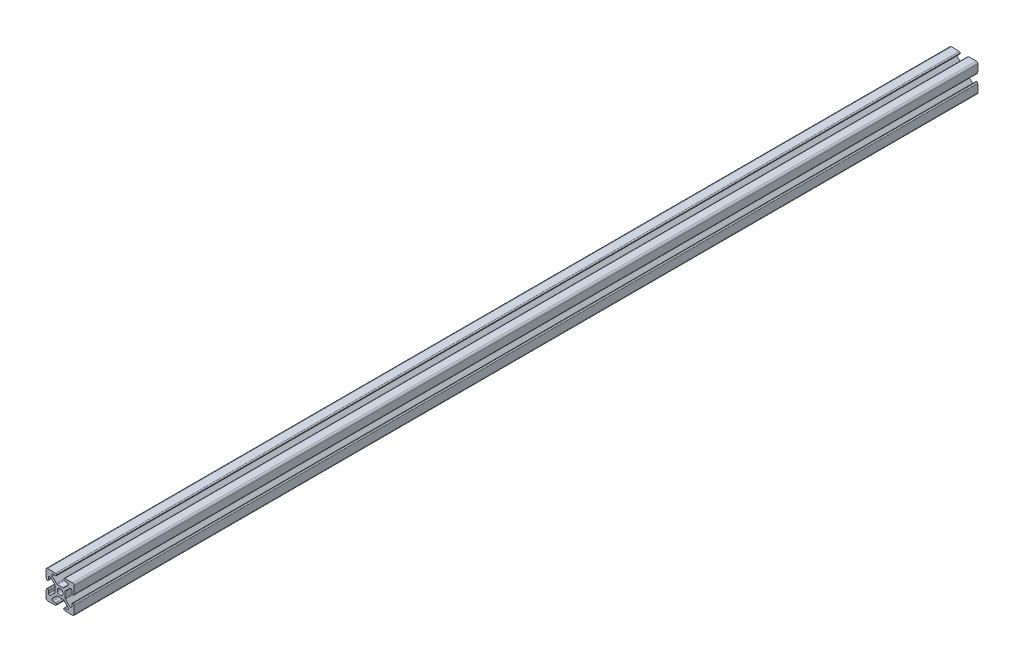
SolidWorks part; units mm, degrees
material "6061 Alloy"
ref_plane "Front Plane" through (0, 0, 0) normal (0, 0, 1) x (1, 0, 0)
ref_plane "Top Plane" through (0, 0, 0) normal (0, 1, 0) x (1, 0, 0)
ref_plane "Right Plane" through (0, 0, 0) normal (1, 0, 0) x (0, 0, -1)
sketch "Sketch1" plane through (0, 0, 0) normal (0, 0, 1) x (1, 0, 0)
  line L1 (3.2385, -11.4554) -> (3.2385, -11.4907)
  line L2 (-7.1065, 8.6691) -> (-3.2584, 4.821)
  line L3 (-3.2385, 11.4907) -> (-3.2385, 11.4554)
  line L6 (-4.2037, 10.4902) -> (-6.3521, 10.4902)
  line L7 (-11.176, 12.7) -> (-4.17, 12.4553)
  line L8 (11.4554, 3.2385) -> (11.4907, 3.2385)
  line L9 (11.4554, -3.2385) -> (11.4907, -3.2385)
  line L11 (-4.821, 3.2584) -> (-8.6691, 7.1065)
  line L12 (-10.4902, 6.3521) -> (-10.4902, 4.2037)
  line L13 (-12.7, 11.176) -> (-12.4553, 4.17)
  line L15 (-4.5085, -2.504) -> (-4.5085, 2.504)
  line L16 (6.3521, -10.4902) -> (4.2037, -10.4902)
  line L22 (-2.504, 4.5085) -> (2.504, 4.5085)
  line L23 (-3.2584, -4.821) -> (-7.1065, -8.6691)
  line L24 (-11.176, -12.7) -> (-4.17, -12.4553)
  line L25 (-12.7, -11.176) -> (-12.4553, -4.17)
  line L26 (-10.4902, -4.2037) -> (-10.4902, -6.3521)
  line L27 (-8.6691, -7.1065) -> (-4.821, -3.2584)
  line L36 (8.6691, -7.1065) -> (4.821, -3.2584)
  line L38 (10.4902, -4.2037) -> (10.4902, -6.3521)
  line L39 (12.7, -11.176) -> (12.4553, -4.17)
  line L42 (11.176, -12.7) -> (4.17, -12.4553)
  line L43 (3.2584, -4.821) -> (7.1065, -8.6691)
  line L47 (4.5085, -2.504) -> (4.5085, 2.504)
  line L48 (12.7, 11.176) -> (12.4553, 4.17)
  line L49 (10.4902, 6.3521) -> (10.4902, 4.2037)
  line L50 (4.821, 3.2584) -> (8.6691, 7.1065)
  line L52 (2.504, -4.5085) -> (-2.504, -4.5085)
  line L56 (11.176, 12.7) -> (4.17, 12.4553)
  line L57 (4.2037, 10.4902) -> (6.3521, 10.4902)
  line L59 (-6.3521, -10.4902) -> (-4.2037, -10.4902)
  line L60 (3.2385, 11.4907) -> (3.2385, 11.4554)
  line L61 (7.1065, 8.6691) -> (3.2584, 4.821)
  line L66 (-11.4554, -3.2385) -> (-11.4907, -3.2385)
  line L68 (-11.4554, 3.2385) -> (-11.4907, 3.2385)
  line L74 (-3.2385, -11.4554) -> (-3.2385, -11.4907)
  arc A1 (-3.2385, 11.4907) -> (-4.17, 12.4553) centre (-4.2037, 11.4907) ccw
  arc A4 (-4.2037, 10.4902) -> (-3.2385, 11.4554) centre (-4.2037, 11.4554) ccw
  arc A6 (-6.3521, 10.4902) -> (-7.1065, 8.6691) centre (-6.3521, 9.4234) ccw
  arc A8 (-12.4553, 4.17) -> (-11.4907, 3.2385) centre (-11.4907, 4.2037) ccw
  arc A9 (-11.176, 12.7) -> (-12.7, 11.176) centre (-11.176, 11.176) ccw
  arc A12 (-8.6691, 7.1065) -> (-10.4902, 6.3521) centre (-9.4234, 6.3521) ccw
  arc A13 (-11.4554, 3.2385) -> (-10.4902, 4.2037) centre (-11.4554, 4.2037) ccw
  arc A16 (-4.821, -3.2584) -> (-4.5085, -2.504) centre (-5.5753, -2.504) ccw
  arc A17 (-4.5085, 2.504) -> (-4.821, 3.2584) centre (-5.5753, 2.504) ccw
  arc A22 (3.2584, 4.821) -> (2.504, 4.5085) centre (2.504, 5.5753) cw
  arc A23 (10.4902, -6.3521) -> (8.6691, -7.1065) centre (9.4234, -6.3521) cw
  arc A24 (10.4902, -4.2037) -> (11.4554, -3.2385) centre (11.4554, -4.2037) cw
  arc A25 (11.4907, -3.2385) -> (12.4553, -4.17) centre (11.4907, -4.2037) cw
  arc A26 (12.7, -11.176) -> (11.176, -12.7) centre (11.176, -11.176) cw
  arc A28 (-2.504, -4.5085) -> (-3.2584, -4.821) centre (-2.504, -5.5753) ccw
  arc A29 (-4.17, -12.4553) -> (-3.2385, -11.4907) centre (-4.2037, -11.4907) ccw
  arc A30 (-3.2385, -11.4554) -> (-4.2037, -10.4902) centre (-4.2037, -11.4554) ccw
  arc A31 (-7.1065, -8.6691) -> (-6.3521, -10.4902) centre (-6.3521, -9.4234) ccw
  arc A32 (-12.7, -11.176) -> (-11.176, -12.7) centre (-11.176, -11.176) ccw
  arc A33 (-11.4907, -3.2385) -> (-12.4553, -4.17) centre (-11.4907, -4.2037) ccw
  arc A34 (-10.4902, -4.2037) -> (-11.4554, -3.2385) centre (-11.4554, -4.2037) ccw
  arc A35 (-10.4902, -6.3521) -> (-8.6691, -7.1065) centre (-9.4234, -6.3521) ccw
  arc A36 (7.1065, -8.6691) -> (6.3521, -10.4902) centre (6.3521, -9.4234) cw
  arc A37 (3.2385, -11.4554) -> (4.2037, -10.4902) centre (4.2037, -11.4554) cw
  arc A38 (-3.2584, 4.821) -> (-2.504, 4.5085) centre (-2.504, 5.5753) ccw
  arc A39 (4.17, -12.4553) -> (3.2385, -11.4907) centre (4.2037, -11.4907) cw
  arc A40 (2.504, -4.5085) -> (3.2584, -4.821) centre (2.504, -5.5753) cw
  circle A44 centre (0, 0) radius 2.5527
  arc A45 (4.5085, 2.504) -> (4.821, 3.2584) centre (5.5753, 2.504) cw
  arc A46 (4.821, -3.2584) -> (4.5085, -2.504) centre (5.5753, -2.504) cw
  arc A47 (11.4554, 3.2385) -> (10.4902, 4.2037) centre (11.4554, 4.2037) cw
  arc A48 (8.6691, 7.1065) -> (10.4902, 6.3521) centre (9.4234, 6.3521) cw
  arc A49 (11.176, 12.7) -> (12.7, 11.176) centre (11.176, 11.176) cw
  arc A53 (12.4553, 4.17) -> (11.4907, 3.2385) centre (11.4907, 4.2037) cw
  arc A54 (6.3521, 10.4902) -> (7.1065, 8.6691) centre (6.3521, 9.4234) cw
  arc A56 (4.2037, 10.4902) -> (3.2385, 11.4554) centre (4.2037, 11.4554) cw
  arc A58 (3.2385, 11.4907) -> (4.17, 12.4553) centre (4.2037, 11.4907) cw
  dimension "D5" = 5.1054
  dimension "D1" = 12.7
  dimension "D2" = 25.4
  dimension "D3" = 25.4
  dimension "D4" = 12.7
extrude "Extrude1" add sketch "Sketch1" along normal blind 812.8
